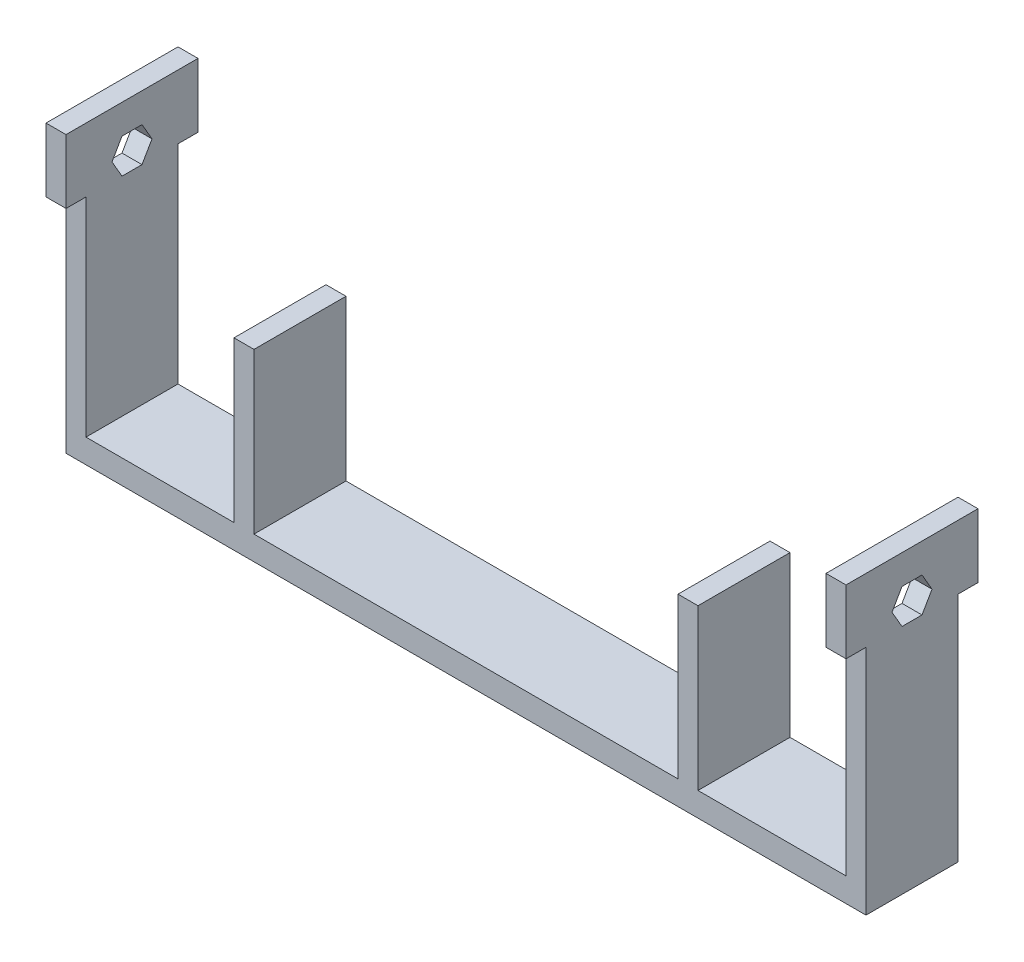
SolidWorks part; units mm, degrees
ref_plane "前视基准面" through (0, 0, 0) normal (0, 0, 1) x (1, 0, 0)
ref_plane "上视基准面" through (0, 0, 0) normal (0, 1, 0) x (1, 0, 0)
ref_plane "右视基准面" through (0, 0, 0) normal (1, 0, 0) x (0, 0, -1)
other "Configuration Table"
sketch "草图1" plane through (0, 0, 0) normal (0, 1, 0) x (1, 0, 0)
  line L1 (0, 0) -> (100, 0)
  line L2 (0, 0) -> (0, 11.5)
  line L3 (0, 11.5) -> (100, 11.5)
  line L4 (100, 0) -> (100, 11.5)
  dimension "D1" = 100
  dimension "D2" = 11.5
extrude "凸台-拉伸1" add sketch "草图1" along normal blind 3
sketch "草图2" plane through (0, 3, 0) normal (0, 1, 0) x (1, 0, 0)
  line L0 (0, 0) -> (100, 0) construction
  line L1 (0, 11.5) -> (2.5, 11.5)
  line L2 (0, 11.5) -> (0, 0)
  line L3 (0, 0) -> (2.5, 0)
  line L4 (2.5, 11.5) -> (2.5, 0)
  line L5 (50, 11.5) -> (50, 24.2128) construction
  line L11 (100, 0) -> (97.5, 0)
  line L12 (97.5, 11.5) -> (97.5, 0)
  line L13 (100, 11.5) -> (97.5, 11.5)
  line L14 (100, 11.5) -> (100, 0)
  dimension "D1" = 2.5
extrude "凸台-拉伸2" add sketch "草图2" along normal blind 26
sketch "草图3" plane through (0, 3, 0) normal (0, 1, 0) x (1, 0, 0)
  line L0 (50, 11.5) -> (50, 23.3213) construction
  line L8 (23.5, 0) -> (21, 0)
  line L9 (21, 11.5) -> (21, 0)
  line L10 (23.5, 11.5) -> (21, 11.5)
  line L11 (23.5, 11.5) -> (23.5, 0)
  line L12 (76.5, 11.5) -> (76.5, 0)
  line L13 (76.5, 11.5) -> (79, 11.5)
  line L14 (79, 11.5) -> (79, 0)
  line L15 (76.5, 0) -> (79, 0)
  dimension "D1" = 18.5
extrude "凸台-拉伸3" add sketch "草图3" along normal blind 20
sketch "草图5" plane through (100, 0, 0) normal (1, 0, 0) x (0, 0, -1)
  line L0 (-1.25, 29) -> (6.7321, 29) construction
  line L2 (5.75, 37) -> (5.75, 41.8559) construction
  line L5 (8.25, 31.1651) -> (7, 33.3301)
  line L6 (7, 33.3301) -> (4.5, 33.3301)
  line L7 (4.5, 33.3301) -> (3.25, 31.1651)
  line L8 (3.25, 31.1651) -> (4.5, 29)
  line L9 (4.5, 29) -> (7, 29)
  line L10 (7, 29) -> (8.25, 31.1651)
  circle A0 centre (5.75, 31.1651) radius 2.1651 construction
  dimension "D1" = 2.5
sketch "草图6" plane through (0, 29, 0) normal (0, 1, 0) x (1, 0, 0)
  line L0 (50, 11.5) -> (50, 26.5767) construction
  line L2 (2.5, 0) -> (2.5, 11.5) construction
  line L3 (0, 14) -> (2.5, 14)
  line L4 (0, 14) -> (0, -2.5)
  line L5 (0, -2.5) -> (2.5, -2.5)
  line L6 (2.5, 14) -> (2.5, -2.5)
  line L7 (0, 11.5) -> (0, 0) construction
  line L8 (100, -2.5) -> (97.5, -2.5)
  line L9 (97.5, 14) -> (97.5, -2.5)
  line L10 (100, 14) -> (97.5, 14)
  line L11 (100, 14) -> (100, -2.5)
  dimension "D1" = 2.5
  dimension "D2" = 2.5
extrude "凸台-拉伸4" add sketch "草图6" along normal blind 8
extrude "切除-拉伸1" cut sketch "草图5" against normal through all
